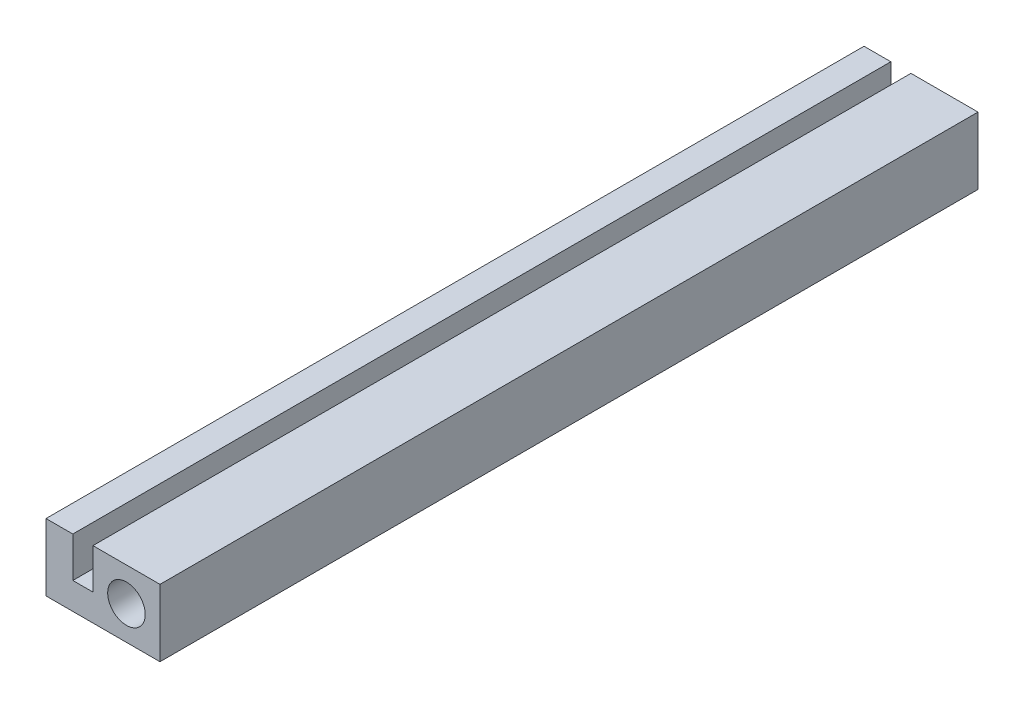
SolidWorks part; units mm, degrees
ref_plane "Plan de face" through (0, 0, 0) normal (0, 0, 1) x (1, 0, 0)
ref_plane "Plan de dessus" through (0, 0, 0) normal (0, 1, 0) x (1, 0, 0)
ref_plane "Plan de droite" through (0, 0, 0) normal (1, 0, 0) x (0, 0, -1)
sketch "Esquisse1" plane through (0, 0, 0) normal (0, 0, 1) x (1, 0, 0)
  line L0 (-6.6767, 2.9371) -> (-6.6767, -7.0629)
  line L1 (-6.6767, -7.0629) -> (10.3233, -7.0629)
  line L2 (10.3233, -7.0629) -> (10.3233, 2.9371)
  line L3 (10.3233, 2.9371) -> (0.3233, 2.9371)
  line L4 (0.3233, 2.9371) -> (0.3233, -3.0629)
  line L5 (0.3233, -3.0629) -> (-2.6767, -3.0629)
  line L6 (-2.6767, -3.0629) -> (-2.6767, 2.9371)
  line L7 (-2.6767, 2.9371) -> (-6.6767, 2.9371)
  line L8 (5.3233, 2.9371) -> (5.3233, -7.0629) construction
  circle A0 centre (5.3233, -2.0629) radius 2.8
  point P8 (-1.1767, -3.0629)
  point P9 (5.3233, 2.9371)
  dimension "D6" = 5.6
  dimension "D1" = 4
  dimension "D2" = 3
  dimension "D3" = 4
  dimension "D4" = 10
  dimension "D5" = 10
extrude "Boss.-Extru.1" add sketch "Esquisse1" along normal blind 122
